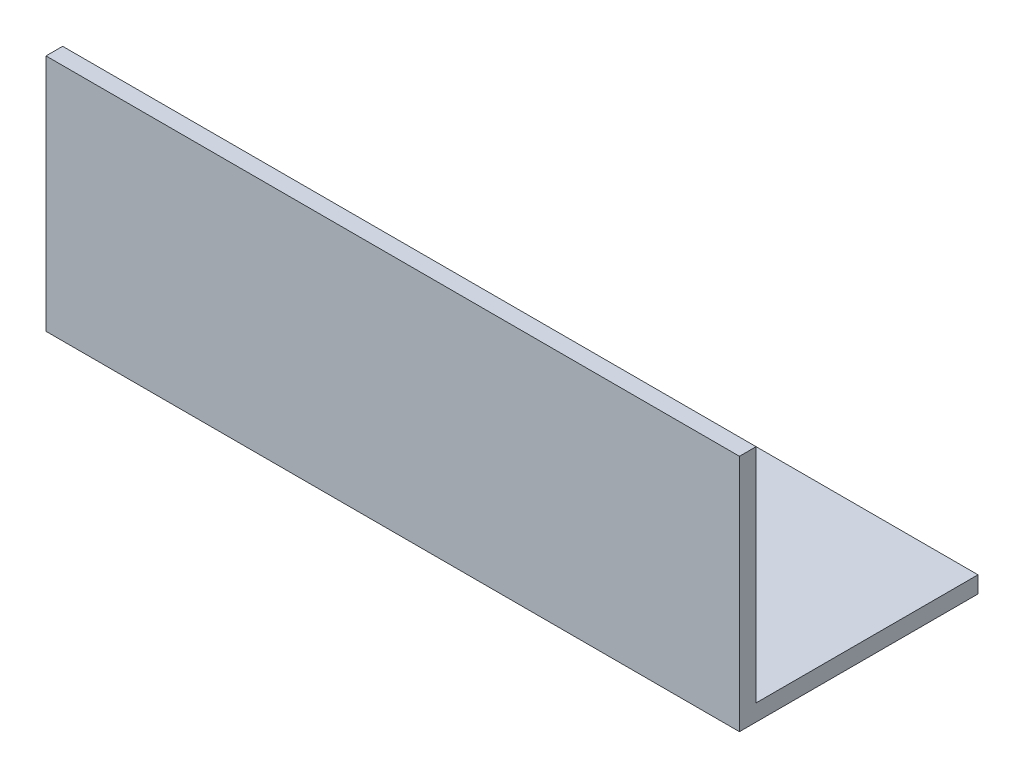
SolidWorks part; units mm, degrees
ref_plane "Спереди" through (0, 0, 0) normal (0, 0, 1) x (1, 0, 0)
ref_plane "Сверху" through (0, 0, 0) normal (0, 1, 0) x (1, 0, 0)
ref_plane "Справа" through (0, 0, 0) normal (1, 0, 0) x (0, 0, -1)
sketch "Эскиз1" plane through (0, 0, 0) normal (1, 0, 0) x (0, 0, -1)
  line L0 (0, 40) -> (0, 0)
  line L1 (0, 0) -> (40, 0)
extrude "Вытянуть-Тонкостенный1" add sketch "Эскиз1" along normal blind 125 thin
